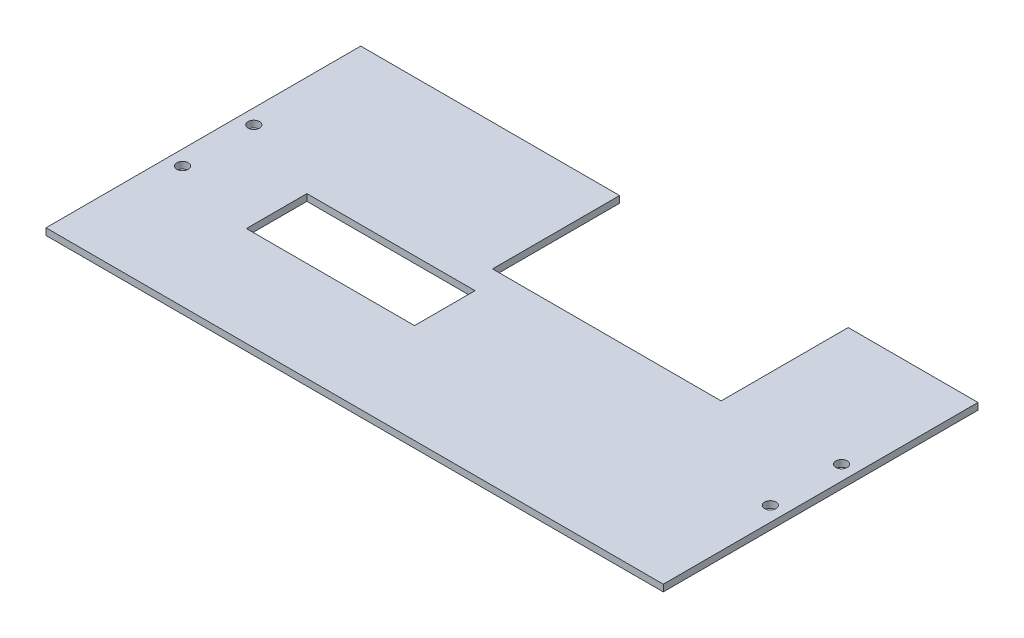
SolidWorks part; units mm, degrees
material "6061-T6 (SS)"
ref_plane "Front Plane" through (0, 0, 0) normal (0, 0, 1) x (1, 0, 0)
ref_plane "Top Plane" through (0, 0, 0) normal (0, 1, 0) x (1, 0, 0)
ref_plane "Right Plane" through (0, 0, 0) normal (1, 0, 0) x (0, 0, -1)
sketch "Sketch1" plane through (0, 0, 0) normal (0, 1, 0) x (1, 0, 0)
  line L1 (-116.586, -59.4402) -> (116.586, -59.4402)
  line L2 (-116.586, -59.4402) -> (-116.586, 59.4402)
  line L3 (-116.586, 59.4402) -> (116.586, 59.4402)
  line L4 (116.586, -59.4402) -> (116.586, 59.4402)
  line L5 (-116.586, -59.4402) -> (116.586, 59.4402) construction
  line L6 (-116.586, 59.4402) -> (116.586, -59.4402) construction
  point P0 (0, 0)
  dimension "D1" = 118.8804
  dimension "D2" = 233.172
extrude "Boss-Extrude1" add sketch "Sketch1" along normal blind 2.54
hole_wizard "#6 Clearance Hole1" positions "Sketch2" profile "Sketch3" hole size "#6" standard "ANSI Inch" end condition through all
sketch "Sketch2" plane through (0, 2.54, 0) normal (0, 1, 0) x (1, 0, 0)
  line L0 (116.586, 59.4402) -> (-116.586, 59.4402) construction
  line L1 (-116.586, 59.4402) -> (-116.586, -59.4402) construction
  line L2 (116.586, -59.4402) -> (116.586, 59.4402) construction
  point P0 (111.0107, 13.4746)
  point P2 (111.0107, -13.4511)
  point P4 (-111.0107, 13.4746)
  point P6 (-111.0107, -13.4511)
  dimension "D1" = 26.9257
  dimension "D2" = 45.9656
  dimension "D3" = 5.5753
  dimension "D4" = 5.5753
sketch "Sketch3" plane through (111.0107, 2.54, -13.4746) normal (1, 0, 0) x (0, 0, 1)
  line L0 (0, 0) -> (0, 2.54)
  line L1 (0, 2.54) -> (2.1526, 2.54)
  line L2 (2.1526, 2.54) -> (2.1526, 0)
  line L5 (2.1526, 0) -> (0, 0)
  line L11 (0, -6.35) -> (0, 107.95) construction
  dimension "Thru Hole Dia." = 4.3053
  dimension "Thru Hole Depth" = 2.54
sketch "Sketch4" plane through (0, 2.54, 0) normal (0, 1, 0) x (1, 0, 0)
  line L0 (116.586, 59.4402) -> (-116.586, 59.4402) construction
  line L1 (-18.8003, 59.4402) -> (67.5597, 59.4402)
  line L2 (-18.8003, 59.4402) -> (-18.8003, 11.4342)
  line L3 (-18.8003, 11.4342) -> (67.5597, 11.4342)
  line L4 (67.5597, 59.4402) -> (67.5597, 11.4342)
  line L5 (-116.586, 59.4402) -> (-116.586, -59.4402) construction
  dimension "D1" = 48.006
  dimension "D2" = 97.7857
  dimension "D3" = 184.1457
extrude "Cut-Extrude1" cut sketch "Sketch4" against normal through all
sketch "Sketch5" plane through (0, 2.54, 0) normal (0, 1, 0) x (1, 0, 0)
  line L0 (-18.8003, 59.4402) -> (-116.586, 59.4402) construction
  line L1 (-78.486, 1.0202) -> (-14.986, 1.0202)
  line L2 (-78.486, 1.0202) -> (-78.486, -21.8398)
  line L3 (-78.486, -21.8398) -> (-14.986, -21.8398)
  line L4 (-14.986, 1.0202) -> (-14.986, -21.8398)
  line L5 (-116.586, 59.4402) -> (-116.586, -59.4402) construction
  dimension "D1" = 58.42
  dimension "D2" = 81.28
  dimension "D3" = 38.1
  dimension "D4" = 101.6
extrude "Cut-Extrude2" cut sketch "Sketch5" against normal through all
